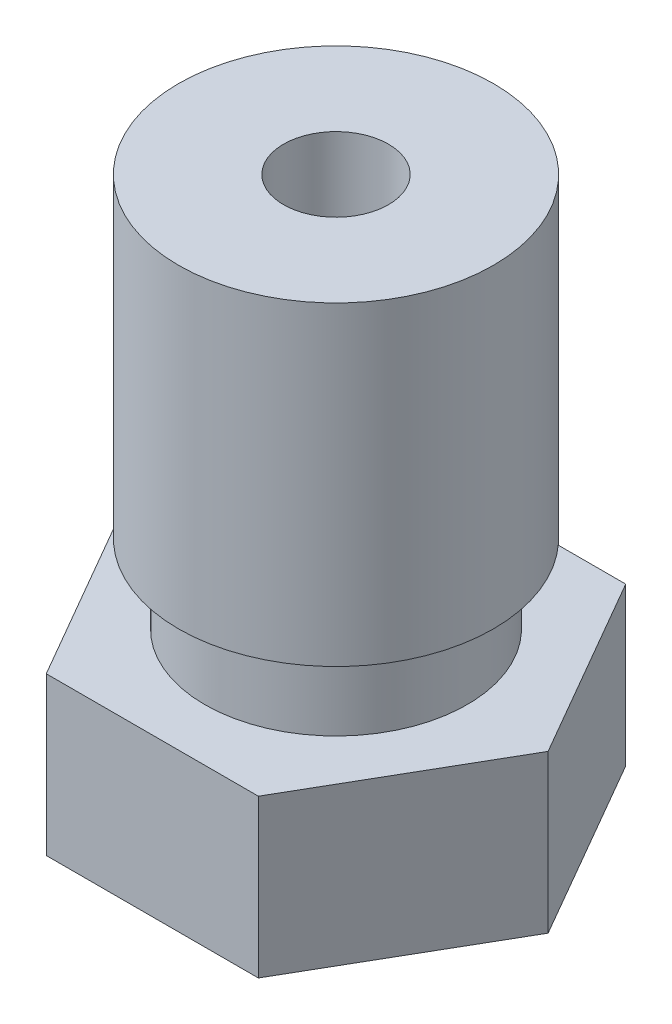
SolidWorks part; units mm, degrees
material "Brass"
ref_plane "Front Plane" through (0, 0, 0) normal (0, 0, 1) x (1, 0, 0)
ref_plane "Top Plane" through (0, 0, 0) normal (0, 1, 0) x (1, 0, 0)
ref_plane "Right Plane" through (0, 0, 0) normal (1, 0, 0) x (0, 0, -1)
sketch "Sketch1" plane through (0, 0, 0) normal (0, 1, 0) x (1, 0, 0)
  line L1 (2.0207, 3.5) -> (-2.0207, 3.5)
  line L2 (-2.0207, 3.5) -> (-4.0415, 0)
  line L3 (-4.0415, 0) -> (-2.0207, -3.5)
  line L4 (-2.0207, -3.5) -> (2.0207, -3.5)
  line L5 (2.0207, -3.5) -> (4.0415, 0)
  line L6 (4.0415, 0) -> (2.0207, 3.5)
  circle A0 centre (0, 0) radius 3.5 construction
  circle A1 centre (0, 0) radius 1
  dimension "D2" = 2
  dimension "D1" = 7
extrude "Boss-Extrude1" add sketch "Sketch1" along normal blind 3
sketch "Sketch2" plane through (0, 0, 0) normal (0, 0, 1) x (1, 0, 0)
  line L0 (1, 0) -> (0.2, -2)
  line L1 (-2.0207, 0) -> (2.0207, 0) construction
  line L2 (0.2, -2) -> (0.5, -2)
  line L3 (0.5, -2) -> (1.9004, 0)
  line L4 (2.0207, 0) -> (4.0415, 0) construction
  line L5 (0, -2) -> (0, 8.8072) construction
  line L6 (1, 0) -> (1.9004, 0)
  line L7 (1, 3) -> (1, 10.5)
  line L8 (-2.0207, 3) -> (2.0207, 3) construction
  line L9 (1, 10.5) -> (3, 10.5)
  line L10 (3, 10.5) -> (3, 4.5)
  line L11 (3, 4.5) -> (2.5, 4.5)
  line L12 (2.5, 4.5) -> (2.5, 3)
  line L13 (2.0207, 3) -> (4.0415, 3) construction
  line L14 (2.5, 3) -> (1, 3)
  line L15 (1, 3) -> (1.0359, 2.9796)
  dimension "D1" = 1
  dimension "D2" = 12.5
  dimension "D3" = 0.4
  dimension "D4" = 125
  dimension "D5" = 7.5
  dimension "D6" = 6
  dimension "D7" = 6
  dimension "D8" = 0.5
  dimension "D9" = 10.5
revolve "Revolve1" add sketch "Sketch2" angle 360 about L5
